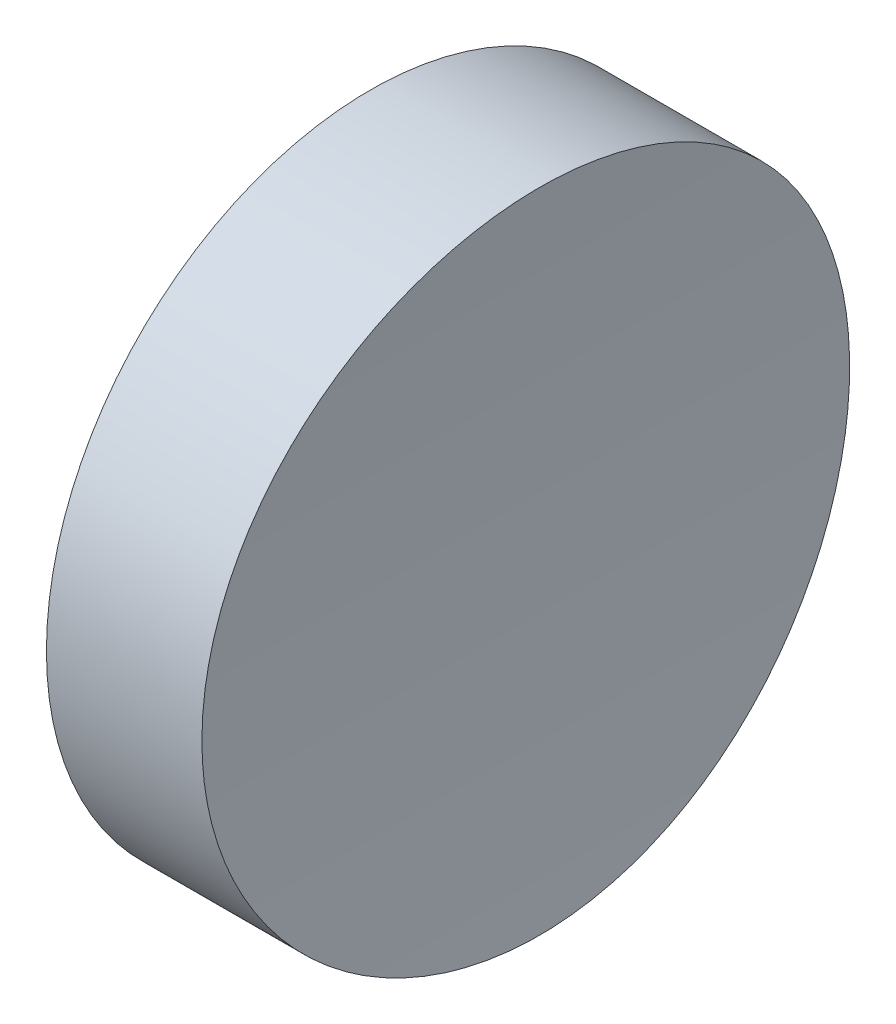
SolidWorks part; units mm, degrees
ref_plane "前视基准面" through (0, 0, 0) normal (0, 0, 1) x (1, 0, 0)
ref_plane "上视基准面" through (0, 0, 0) normal (0, 1, 0) x (1, 0, 0)
ref_plane "右视基准面" through (0, 0, 0) normal (1, 0, 0) x (0, 0, -1)
sketch "草图1" plane through (0, 0, 0) normal (1, 0, 0) x (0, 0, -1)
  circle A0 centre (0, 0) radius 12.5
  dimension "D1" = 25
extrude "凸台-拉伸1" add sketch "草图1" along normal blind 10
sketch "草图2" plane through (0, 0, 0) normal (0, 0, 1) x (1, 0, 0)
  line L0 (0, 0) -> (156, 0) construction
  line L1 (0, 0) -> (6, 0) construction
  circle A0 centre (156, 0) radius 150
  dimension "D1" = 300
  dimension "D2" = 6
extrude "切除-拉伸1" cut sketch "草图2" against normal through all both and the other way through all
